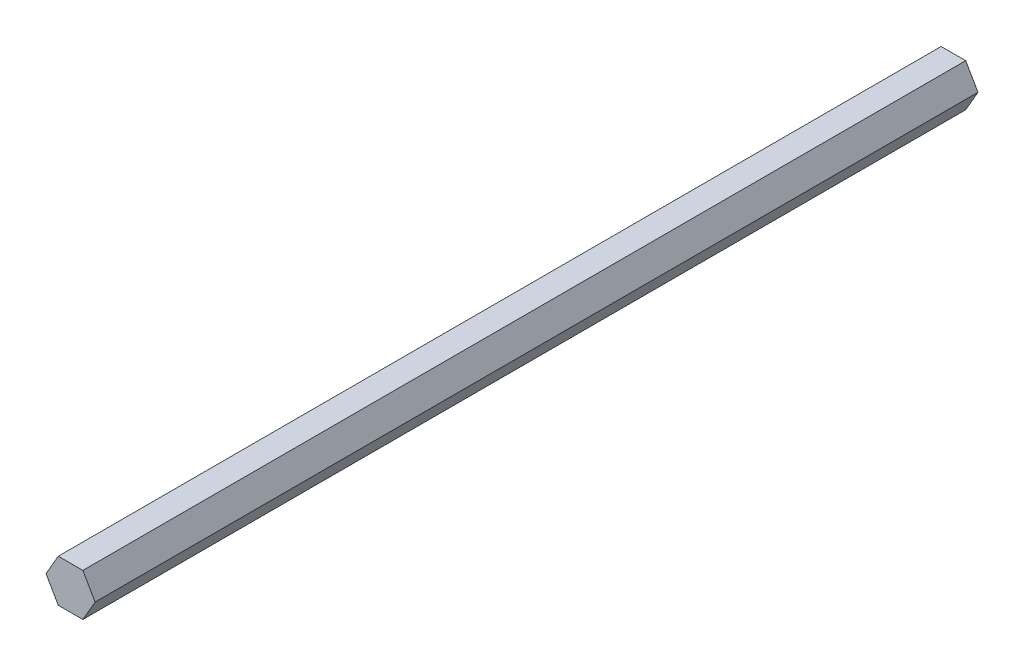
SolidWorks part; units mm, degrees
ref_plane "Front Plane" through (0, 0, 0) normal (0, 0, 1) x (1, 0, 0)
ref_plane "Top Plane" through (0, 0, 0) normal (0, 1, 0) x (1, 0, 0)
ref_plane "Right Plane" through (0, 0, 0) normal (1, 0, 0) x (0, 0, -1)
sketch "Sketch1" plane through (0, 0, 0) normal (0, 0, 1) x (1, 0, 0)
  line L1 (7.3323, 0) -> (3.6662, 6.35)
  line L2 (3.6662, 6.35) -> (-3.6662, 6.35)
  line L3 (-3.6662, 6.35) -> (-7.3323, 0)
  line L4 (-7.3323, 0) -> (-3.6662, -6.35)
  line L5 (-3.6662, -6.35) -> (3.6662, -6.35)
  line L6 (3.6662, -6.35) -> (7.3323, 0)
  circle A0 centre (0, 0) radius 6.35 construction
  dimension "D1" = 12.7
extrude "Boss-Extrude1" add sketch "Sketch1" along normal blind 263.525
